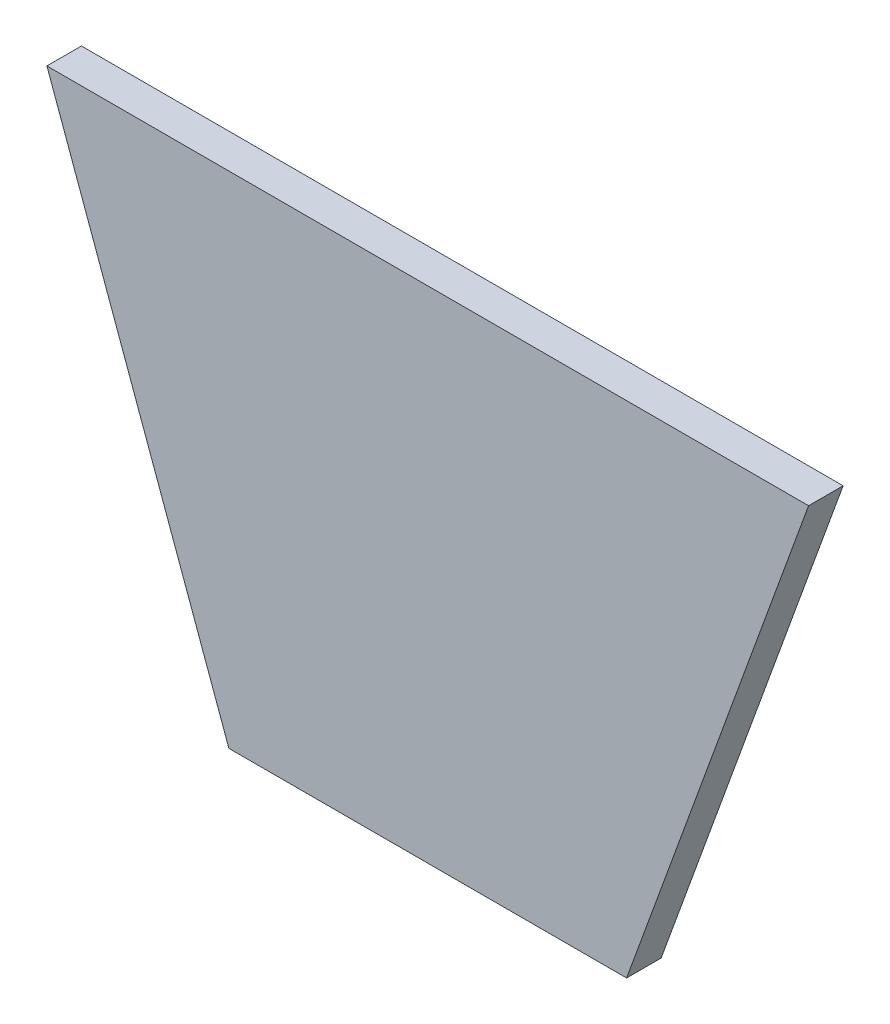
SolidWorks part; units mm, degrees
ref_plane "Front Plane" through (0, 0, 0) normal (0, 0, 1) x (1, 0, 0)
ref_plane "Top Plane" through (0, 0, 0) normal (0, 1, 0) x (1, 0, 0)
ref_plane "Right Plane" through (0, 0, 0) normal (1, 0, 0) x (0, 0, -1)
sketch "Sketch1" plane through (0, 0, 0) normal (0, 0, 1) x (1, 0, 0)
  line L0 (13.0812, 148.0261) -> (-53.0812, 148.0261)
  line L1 (-53.0812, 148.0261) -> (-37.2742, 104.5966)
  line L2 (-37.2742, 104.5966) -> (-2.7258, 104.5966)
  line L3 (0.0933, 103.5705) -> (-2.7258, 104.5966) construction
  line L4 (-2.7258, 104.5966) -> (13.0812, 148.0261) construction
  line L5 (-2.7258, 104.5966) -> (13.0812, 148.0261)
  line L6 (-37.2742, 104.5966) -> (-40.0933, 103.5705) construction
  line L7 (-37.2742, 104.5966) -> (-53.0812, 148.0261) construction
extrude "Boss-Extrude1" add sketch "Sketch1" along normal blind 3
